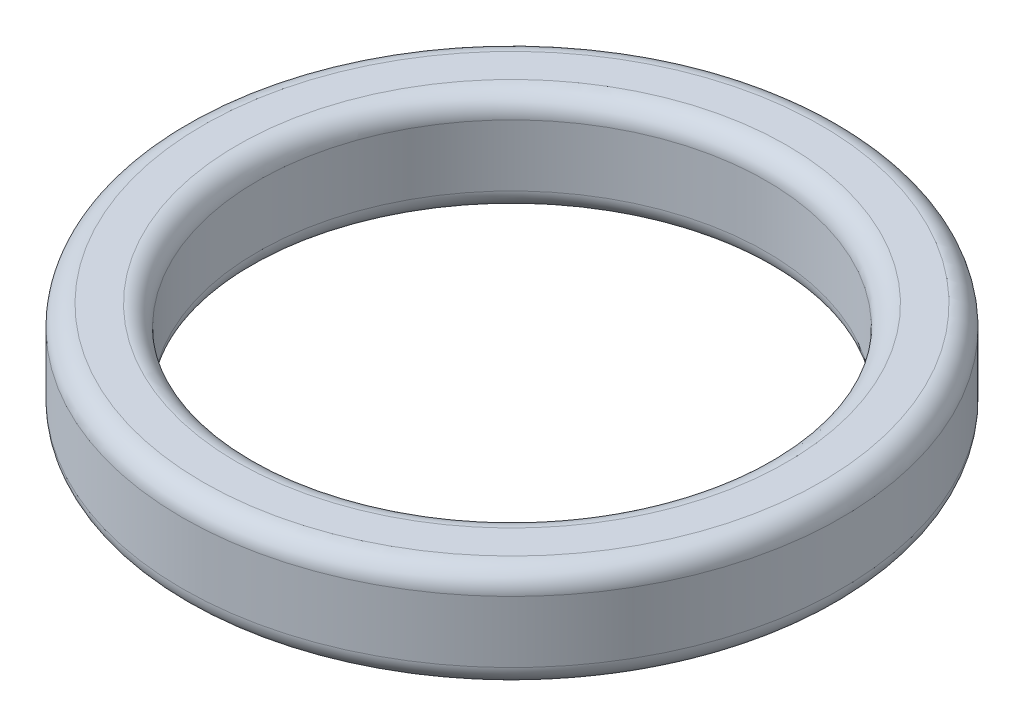
SolidWorks part; units mm, degrees
ref_plane "Front Plane" through (0, 0, 0) normal (0, 0, 1) x (1, 0, 0)
ref_plane "Top Plane" through (0, 0, 0) normal (0, 1, 0) x (1, 0, 0)
ref_plane "Right Plane" through (0, 0, 0) normal (1, 0, 0) x (0, 0, -1)
sketch "Sketch1" plane through (0, 0, 0) normal (0, 1, 0) x (1, 0, 0)
  circle A0 centre (0, 0) radius 32.122
  circle A1 centre (0, 0) radius 24.7757
extrude "Extrude1" add sketch "Sketch1" along normal blind 10
fillet "Fillet1" radius 2 4 edges at (0, 0, 24.7757) (0, 10, 24.7757) (0, 0, 32.122) (0, 10, 32.122)
